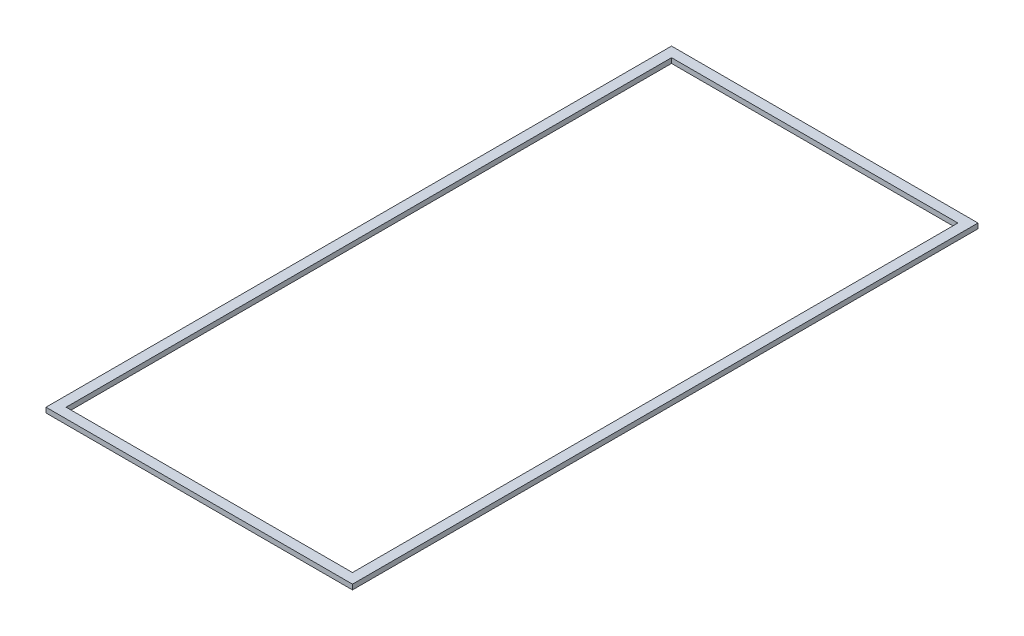
SolidWorks part; units mm, degrees
ref_plane "Спереди" through (0, 0, 0) normal (0, 0, 1) x (1, 0, 0)
ref_plane "Сверху" through (0, 0, 0) normal (0, 1, 0) x (1, 0, 0)
ref_plane "Справа" through (0, 0, 0) normal (1, 0, 0) x (0, 0, -1)
sketch "Эскиз1" plane through (0, 0, 0) normal (0, 1, 0) x (1, 0, 0)
  line L1 (0, 0) -> (610, 0)
  line L2 (0, 0) -> (0, 1245)
  line L3 (0, 1245) -> (610, 1245)
  line L4 (610, 0) -> (610, 1245)
extrude "Вытянуть-Тонкостенный1" add sketch "Эскиз1" along normal blind 10 thin thin type one direction reverse wall 20
